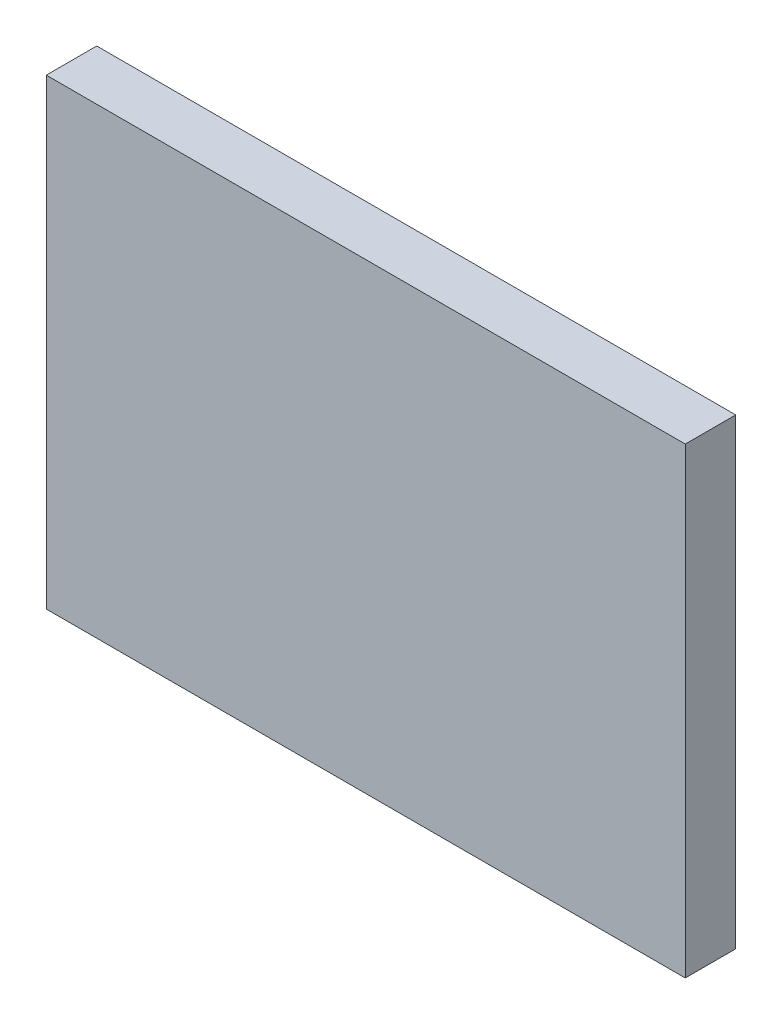
SolidWorks part; units mm, degrees
ref_plane "Front Plane" through (0, 0, 0) normal (0, 0, 1) x (1, 0, 0)
ref_plane "Top Plane" through (0, 0, 0) normal (0, 1, 0) x (1, 0, 0)
ref_plane "Right Plane" through (0, 0, 0) normal (1, 0, 0) x (0, 0, -1)
sketch "Sketch1" plane through (0, 0, 0) normal (0, 0, 1) x (1, 0, 0)
  line L7 (-19, -49.5218) -> (19, -49.5218)
  line L8 (-19, -49.5218) -> (-19, -77.0218)
  line L9 (-19, -77.0218) -> (19, -77.0218)
  line L10 (19, -49.5218) -> (19, -77.0218)
extrude "Boss-Extrude1" add sketch "Sketch1" along normal blind 3
